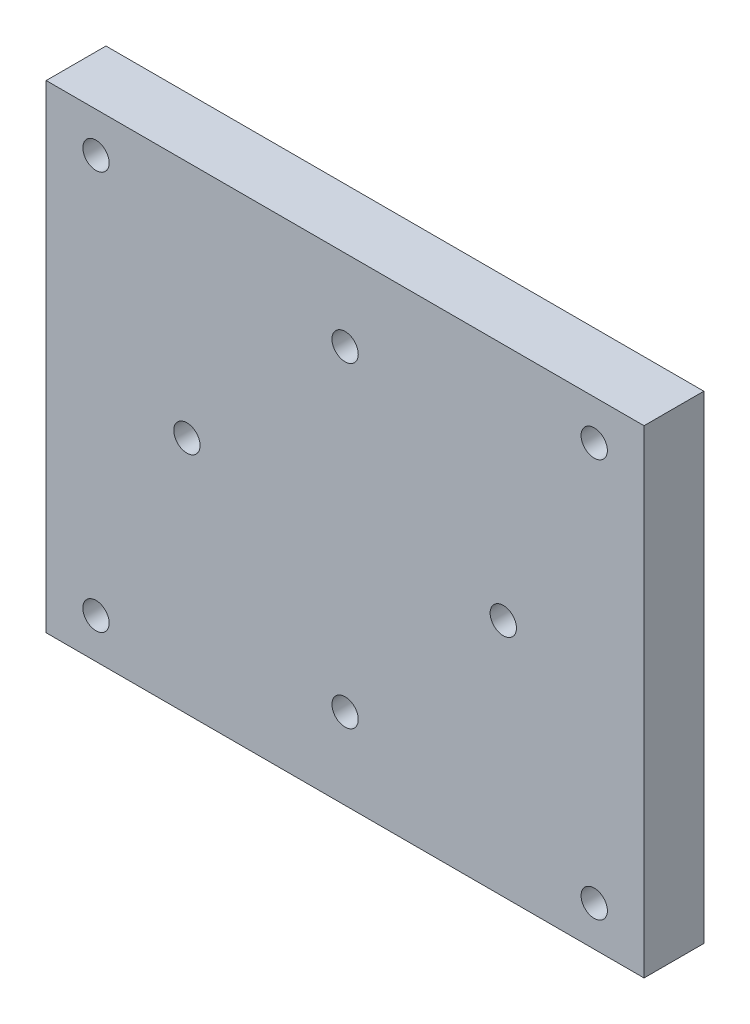
SolidWorks part; units mm, degrees
ref_plane "Front Plane" through (0, 0, 0) normal (0, 0, 1) x (1, 0, 0)
ref_plane "Top Plane" through (0, 0, 0) normal (0, 1, 0) x (1, 0, 0)
ref_plane "Right Plane" through (0, 0, 0) normal (1, 0, 0) x (0, 0, -1)
sketch "Sketch1" plane through (0, 0, 0) normal (0, 0, 1) x (1, 0, 0)
  line L0 (-30, 24) -> (30, -24) construction
  line L1 (30, 24) -> (-30, 24)
  line L2 (30, 24) -> (30, -24)
  line L3 (30, -24) -> (-30, -24)
  line L4 (-30, 24) -> (-30, -24)
  line L5 (30, 24) -> (-30, -24) construction
  line L6 (0, 0) -> (0, -26.0057) construction
  line L7 (0.5075, 0) -> (50000.5075, 0) construction
  line L8 (0, 0) -> (0, -50000) construction
  line L9 (-25, 20) -> (25, -20) construction
  line L10 (0, 0) -> (5.2736, 3.5775) construction
  line L13 (-25, -20) -> (25, -20) construction
  line L14 (25, -20) -> (25, 20) construction
  line L15 (25, 20) -> (-25, 20) construction
  line L16 (-25, 20) -> (-25, -20) construction
  circle A0 centre (0, -15.875) radius 1.32
  circle A1 centre (-15.875, 0) radius 1.32
  circle A2 centre (0, 15.875) radius 1.32
  circle A3 centre (15.875, 0) radius 1.32
  circle A4 centre (-25, 20) radius 1.32
  circle A5 centre (25, 20) radius 1.32
  circle A6 centre (25, -20) radius 1.32
  circle A7 centre (-25, -20) radius 1.32
  point P29 (0, 0)
  dimension "D3" = 2.64
  dimension "D10" = 2.64
  dimension "D13" = 50
  dimension "D14" = 40
  dimension "D1" = 60
  dimension "D2" = 48
  dimension "D4" = 15.875
  dimension "D11" = 2
  dimension "D12" = 2
  dimension "D5" = 4
extrude "Boss-Extrude1" add sketch "Sketch1" along normal blind 6
sketch "Sketch2" plane through (0, 0, 0) normal (0, 0, -1) x (-1, 0, 0)
  circle A0 centre (0, 15.875) radius 3.25
  circle A1 centre (0, 15.875) radius 1.32 construction
  circle A2 centre (15.875, 0) radius 3.25
  circle A3 centre (0, -15.875) radius 3.25
  circle A4 centre (-15.875, 0) radius 3.25
  point P14 (0, 0)
  dimension "D1" = 6.5
  dimension "D2" = 4
extrude "Cut-Extrude1" cut sketch "Sketch2" against normal blind 4
